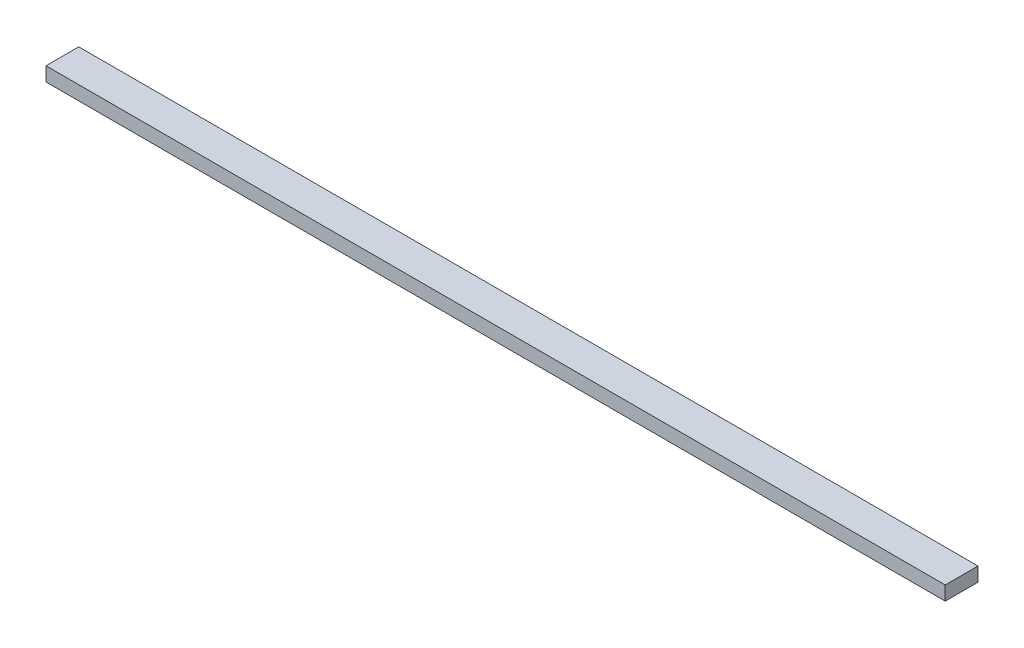
SolidWorks part; units mm, degrees
ref_plane "Front Plane" through (0, 0, 0) normal (0, 0, 1) x (1, 0, 0)
ref_plane "Top Plane" through (0, 0, 0) normal (0, 1, 0) x (1, 0, 0)
ref_plane "Right Plane" through (0, 0, 0) normal (1, 0, 0) x (0, 0, -1)
sketch "Sketch1" plane through (0, 0, 0) normal (0, 1, 0) x (1, 0, 0)
  line L1 (0, 0) -> (2438.4, 0)
  line L2 (0, 0) -> (0, -88.9)
  line L3 (0, -88.9) -> (2438.4, -88.9)
  line L4 (2438.4, 0) -> (2438.4, -88.9)
extrude "Boss-Extrude1" add sketch "Sketch1" along normal blind 38.1
sketch "Sketch2" plane through (0, 0, 0) normal (0, -1, 0) x (1, 0, 0)
  line L0 (1219.2, 88.9) -> (1219.2, 0) construction
  line L1 (0, 88.9) -> (2438.4, 88.9) construction
  line L2 (2438.4, 0) -> (0, 0) construction
  line L3 (1219.2, 44.45) -> (1238.25, 44.45) construction
  line L4 (1219.2, 44.45) -> (1200.15, 44.45) construction
  line L5 (1238.25, 88.9) -> (1238.25, 0) construction
  line L6 (1200.15, 88.9) -> (1200.15, 0) construction
